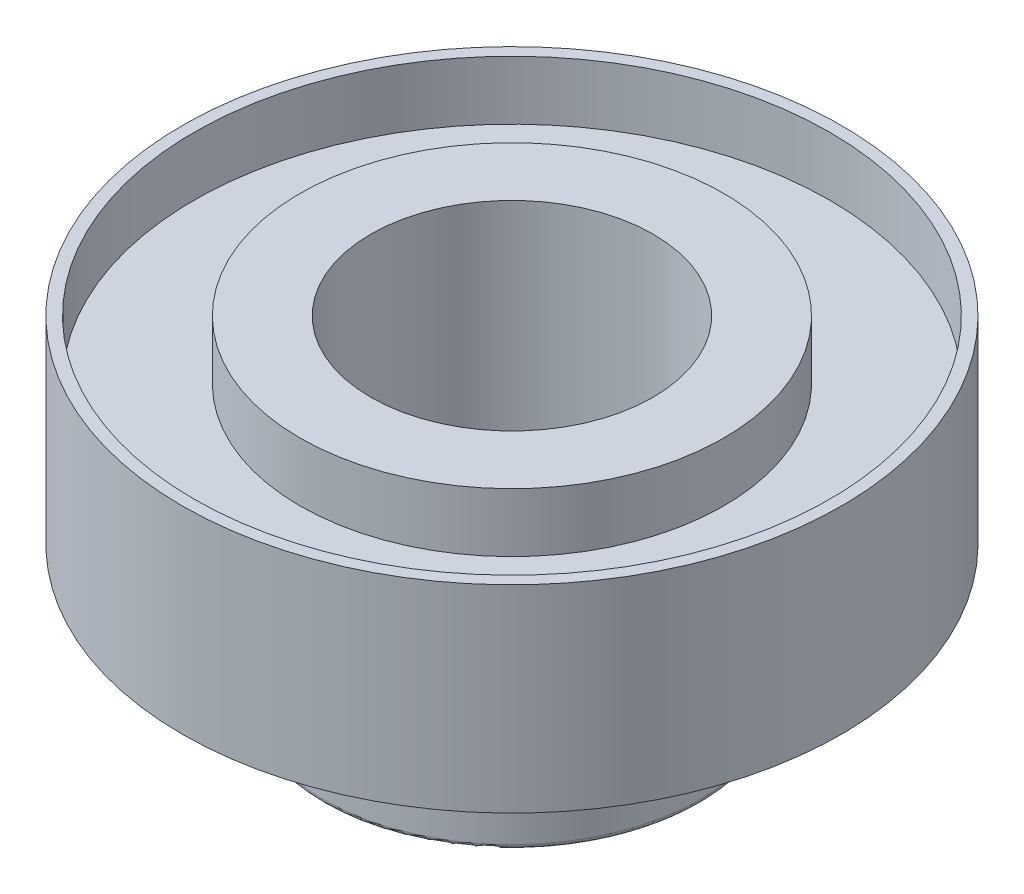
SolidWorks part; units mm, degrees
ref_plane "Front Plane" through (0, 0, 0) normal (0, 0, 1) x (1, 0, 0)
ref_plane "Top Plane" through (0, 0, 0) normal (0, 1, 0) x (1, 0, 0)
ref_plane "Right Plane" through (0, 0, 0) normal (1, 0, 0) x (0, 0, -1)
sketch "Sketch1" plane through (0, 0, 0) normal (0, 1, 0) x (1, 0, 0)
  circle A0 centre (0, 0) radius 7
  dimension "D1" = 14
extrude "Boss-Extrude1" add sketch "Sketch1" along normal blind 4.2
sketch "Sketch2" plane through (0, 4.2, 0) normal (0, 1, 0) x (1, 0, 0)
  circle A0 centre (0, 0) radius 3
  dimension "D1" = 6
extrude "Cut-Extrude1" cut sketch "Sketch2" against normal blind 4.2
sketch "Sketch3" plane through (0, 4.2, 0) normal (0, 1, 0) x (1, 0, 0)
  circle A0 centre (0, 0) radius 6.75
  circle A1 centre (0, 0) radius 4.5
  dimension "D1" = 9
  dimension "D2" = 13.5
extrude "Cut-Extrude2" cut sketch "Sketch3" against normal blind 1.25
sketch "Sketch4" plane through (0, 0, 0) normal (0, -1, 0) x (1, 0, 0)
  circle A0 centre (0, 0) radius 3
  circle A1 centre (0, 0) radius 4
  dimension "D1" = 6
  dimension "D2" = 8
extrude "Boss-Extrude2" add sketch "Sketch4" along normal blind 2.8
fillet "Fillet1" radius 0.1 1 edges at (0, -2.8, -4)
